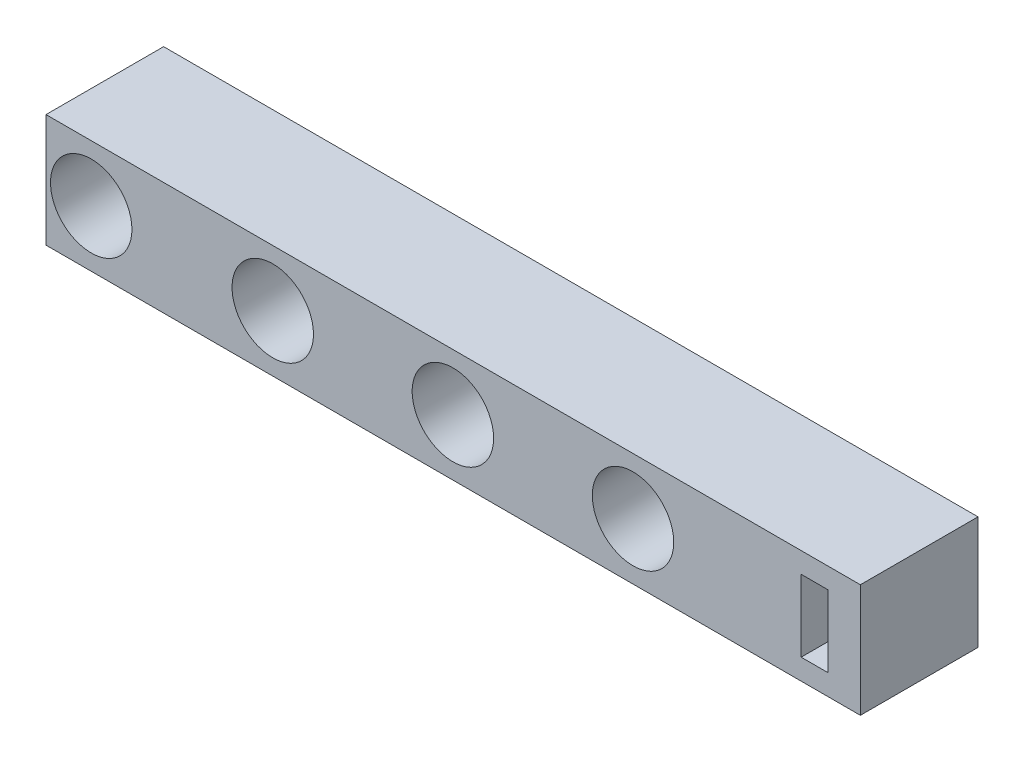
SolidWorks part; units mm, degrees
ref_plane "Ebene vorne" through (0, 0, 0) normal (0, 0, 1) x (1, 0, 0)
ref_plane "Ebene oben" through (0, 0, 0) normal (0, 1, 0) x (1, 0, 0)
ref_plane "Ebene rechts" through (0, 0, 0) normal (1, 0, 0) x (0, 0, -1)
sketch "Skizze1" plane through (0, 0, 0) normal (0, 0, 1) x (1, 0, 0)
  line L0 (20, 32.4365) -> (20, -11.0179) construction
  line L1 (0, 0) -> (180, 0)
  line L2 (0, 0) -> (0, 25)
  line L3 (0, 25) -> (180, 25)
  line L4 (180, 0) -> (180, 25)
  line L5 (40, 32.4365) -> (40, -11.0179) construction
  line L6 (60, 32.4365) -> (60, -11.0179) construction
  line L7 (80, 32.4365) -> (80, -11.0179) construction
  line L8 (100, 32.4365) -> (100, -11.0179) construction
  line L9 (120, 32.4365) -> (120, -11.0179) construction
  line L10 (140, 32.4365) -> (140, -11.0179) construction
  line L11 (160, 32.4365) -> (160, -11.0179) construction
  dimension "D1" = 180
  dimension "D2" = 25
  dimension "D3" = 20
  dimension "D4" = 20
  dimension "D5" = 20
  dimension "D6" = 20
  dimension "D7" = 20
  dimension "D8" = 20
  dimension "D9" = 20
  dimension "D10" = 20
extrude "Aufsatz-Linear austragen1" add sketch "Skizze1" along normal blind 26
hole_wizard "Ø18.0 (18) Durchmesser Bohrung2" positions "Skizze7" profile "Skizze8" hole size "Ø18.0" standard "DIN" end condition through all
sketch "Skizze7" plane through (0, 0, 26) normal (0, 0, 1) x (1, 0, 0)
  point P0 (9.9956, 12.5)
  point P2 (50.1213, 12.5)
  point P4 (89.9347, 12.5)
  point P6 (129.7481, 12.5)
sketch "Skizze8" plane through (9.9956, 12.5, 26) normal (1, 0, 0) x (0, -1, 0)
  line L0 (0, 0) -> (0, 26)
  line L1 (0, 26) -> (9, 26)
  line L2 (9, 26) -> (9, 0)
  line L5 (9, 0) -> (0, 0)
  line L11 (0, -6.35) -> (0, 107.95) construction
  dimension "Bohrerdurchmesser" = 18
  dimension "Bohrungstiefe" = 26
sketch "Skizze9" plane through (0, 0, 26) normal (0, 0, 1) x (1, 0, 0)
  line L1 (172.8107, 20.4583) -> (166.9131, 20.4583)
  line L2 (172.8107, 20.4583) -> (172.8107, 4.591)
  line L3 (172.8107, 4.591) -> (166.9131, 4.591)
  line L4 (166.9131, 20.4583) -> (166.9131, 4.591)
  dimension "D1" = 15.8673
  dimension "D2" = 5.8976
extrude "Schnitt-Linear austragen1" cut sketch "Skizze9" against normal through all
